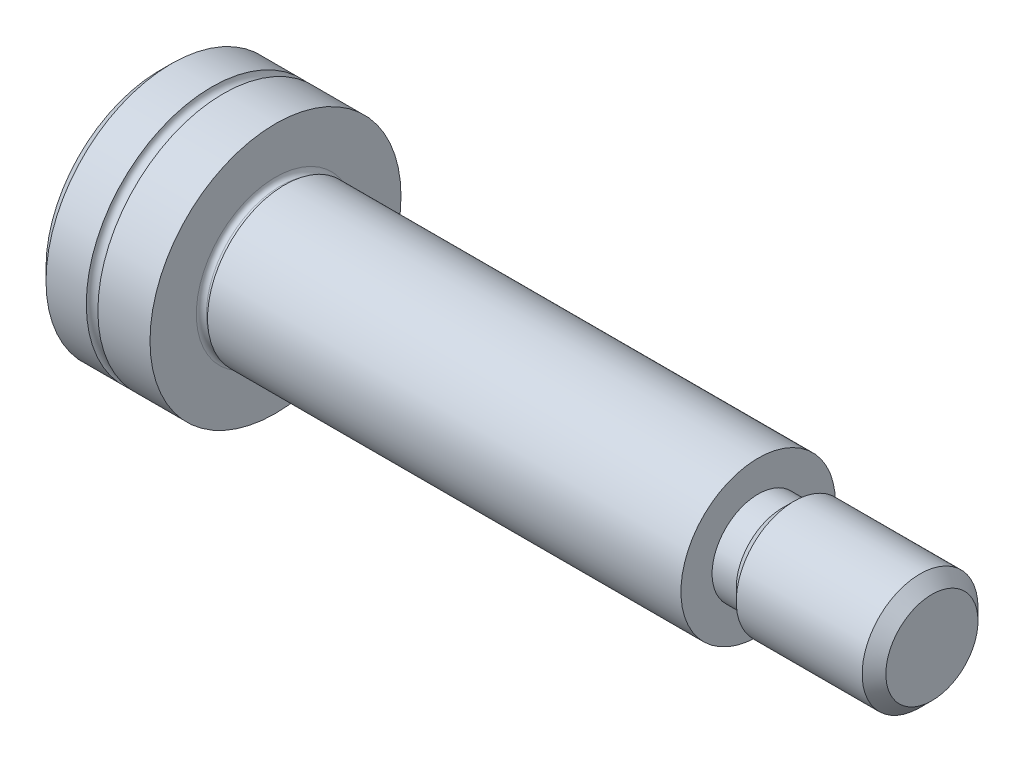
SolidWorks part; units mm, degrees
material "AISI 304"
ref_plane "Front Plane" through (0, 0, 0) normal (0, 0, 1) x (1, 0, 0)
ref_plane "Top Plane" through (0, 0, 0) normal (0, 1, 0) x (1, 0, 0)
ref_plane "Right Plane" through (0, 0, 0) normal (1, 0, 0) x (0, 0, -1)
ref_plane "Plane1" through (0, 0, 0) normal (0, 0, -1) x (-1, 0, 0)
sketch "Sketch1" plane through (0, 0, 0) normal (0, 0, -1) x (-1, 0, 0)
  line L0 (0, 6.5) -> (0, 0)
  line L1 (0, 0) -> (6, 0)
  line L2 (6, 0) -> (6, 6.5)
  line L3 (6, 6.5) -> (3.3, 6.5)
  line L4 (2.7, 6.5) -> (0, 6.5)
  line L5 (0, 0) -> (6, 0) construction
  arc A0 (3.3, 6.5) -> (2.7, 6.5) centre (3, 6.5) cw
revolve "Revolve1" add sketch "Sketch1" angle 360 about L5
sketch "Sketch2" plane through (0, 0, 0) normal (1, 0, 0) x (0, 0, -1)
  circle A0 centre (0, 0) radius 3.84
extrude "Boss-Extrude1" add sketch "Sketch2" along normal blind 0.3876
sketch "Sketch3" plane through (0.3876, 0, 0) normal (1, 0, 0) x (0, 0, -1)
  circle A0 centre (0, 0) radius 3.84
extrude "Boss-Extrude2" add sketch "Sketch3" along normal blind 0.0924 draft 60 draft outward yes
sketch "Sketch4" plane through (0.48, 0, 0) normal (1, 0, 0) x (0, 0, -1)
  circle A0 centre (0, 0) radius 4
extrude "Boss-Extrude3" add sketch "Sketch4" along normal blind 24.52
sketch "Sketch5" plane through (25, 0, 0) normal (1, 0, 0) x (0, 0, -1)
  circle A0 centre (0, 0) radius 2.3865
extrude "Boss-Extrude4" add sketch "Sketch5" along normal blind 1.25
sketch "Sketch6" plane through (26.25, 0, 0) normal (1, 0, 0) x (0, 0, -1)
  circle A0 centre (0, 0) radius 2.3865
extrude "Boss-Extrude5" add sketch "Sketch6" along normal blind 0.6135 draft 45 draft outward yes
sketch "Sketch7" plane through (26.8635, 0, 0) normal (1, 0, 0) x (0, 0, -1)
  circle A0 centre (0, 0) radius 3
extrude "Boss-Extrude6" add sketch "Sketch7" along normal blind 7.1365
sketch "Sketch8" plane through (-6, 0, 0) normal (-1, 0, 0) x (0, 0, 1)
  line L0 (2.5, -1.4434) -> (2.5, 1.4434)
  line L1 (2.5, 1.4434) -> (0, 2.8868)
  line L2 (0, 2.8868) -> (-2.5, 1.4434)
  line L3 (-2.5, 1.4434) -> (-2.5, -1.4434)
  line L4 (-2.5, -1.4434) -> (0, -2.8868)
  line L5 (0, -2.8868) -> (2.5, -1.4434)
extrude "Cut-Extrude1" cut sketch "Sketch8" against normal blind 3
sketch "Sketch9" plane through (0, 0, 0) normal (0, 0, 1) x (1, 0, 0)
  line L0 (-3, 2.4) -> (-3, 0)
  line L1 (-3, 0) -> (-1.6144, 0)
  line L2 (-1.6144, 0) -> (-3, 2.4)
  line L3 (-3, 0) -> (-1.6144, 0) construction
revolve "Cut-Revolve1" cut sketch "Sketch9" angle 360 about L3
chamfer "Chamfer1" distance 0.6135 angle 45 2 edges at (-6, 0, 6.5) (34, 0, -3)
fillet "Fillet1" radius 0.261 1 edges at (0, 0, -3.84)
